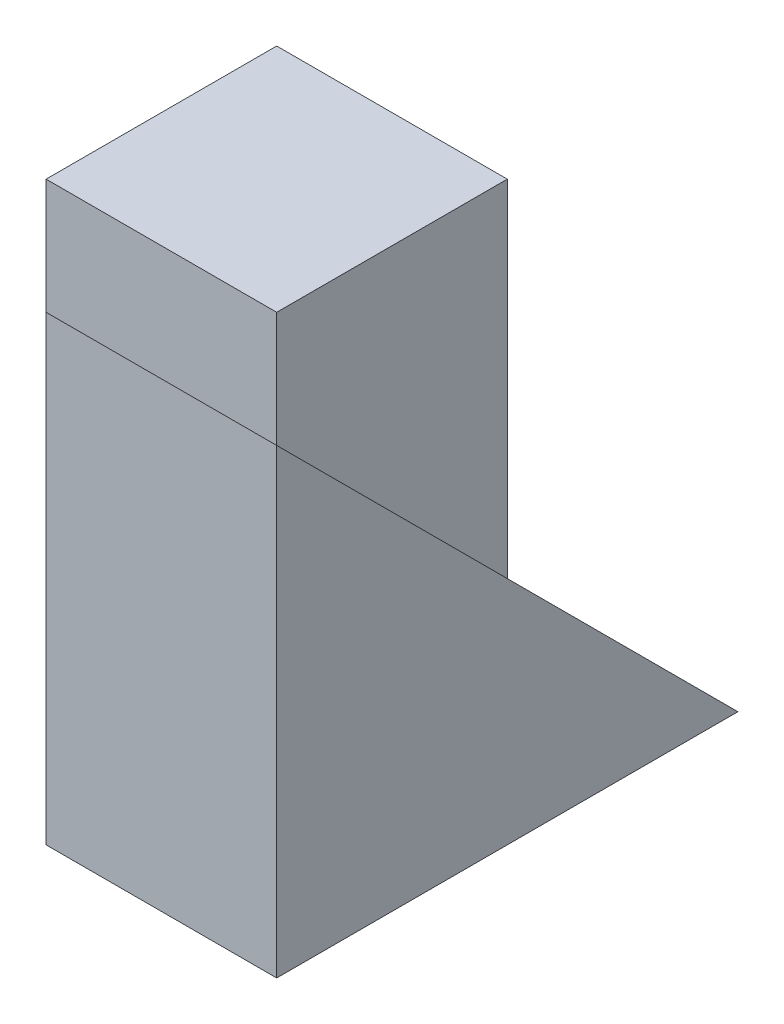
SolidWorks part; units mm, degrees
ref_plane "Front Plane" through (0, 0, 0) normal (0, 0, 1) x (1, 0, 0)
ref_plane "Top Plane" through (0, 0, 0) normal (0, 1, 0) x (1, 0, 0)
ref_plane "Right Plane" through (0, 0, 0) normal (1, 0, 0) x (0, 0, -1)
sketch "Sketch1" plane through (0, 0, 0) normal (1, 0, 0) x (0, 0, -1)
  line L1 (0, 0) -> (4, 0)
  line L2 (0, 0) -> (0, 4)
  line L3 (0, 4) -> (4, 4)
  line L4 (4, 0) -> (4, 4)
  dimension "D1" = 4
  dimension "D2" = 4
extrude "Boss-Extrude1" add sketch "Sketch1" along normal blind 2
sketch "Sketch2" plane through (0, 0, 0) normal (-1, 0, 0) x (0, 0, 1)
  line L1 (-4, 0) -> (-2, 0)
  line L2 (-4, 0) -> (-4, 3)
  line L3 (-4, 3) -> (-2, 3)
  line L4 (-2, 0) -> (-2, 3)
  dimension "D1" = 3
  dimension "D2" = 2
extrude "Boss-Extrude2" add sketch "Sketch2" along normal blind 2
sketch "Sketch3" plane through (2, 0, 0) normal (1, 0, 0) x (0, 0, -1)
  line L0 (0, 4) -> (4, 0)
  line L1 (4, 0) -> (4, 4)
  line L2 (4, 0) -> (4, 4) construction
  line L3 (4, 4) -> (0, 4) construction
  line L4 (4, 4) -> (0, 4)
extrude "Cut-Extrude2" cut sketch "Sketch3" against normal blind 2
